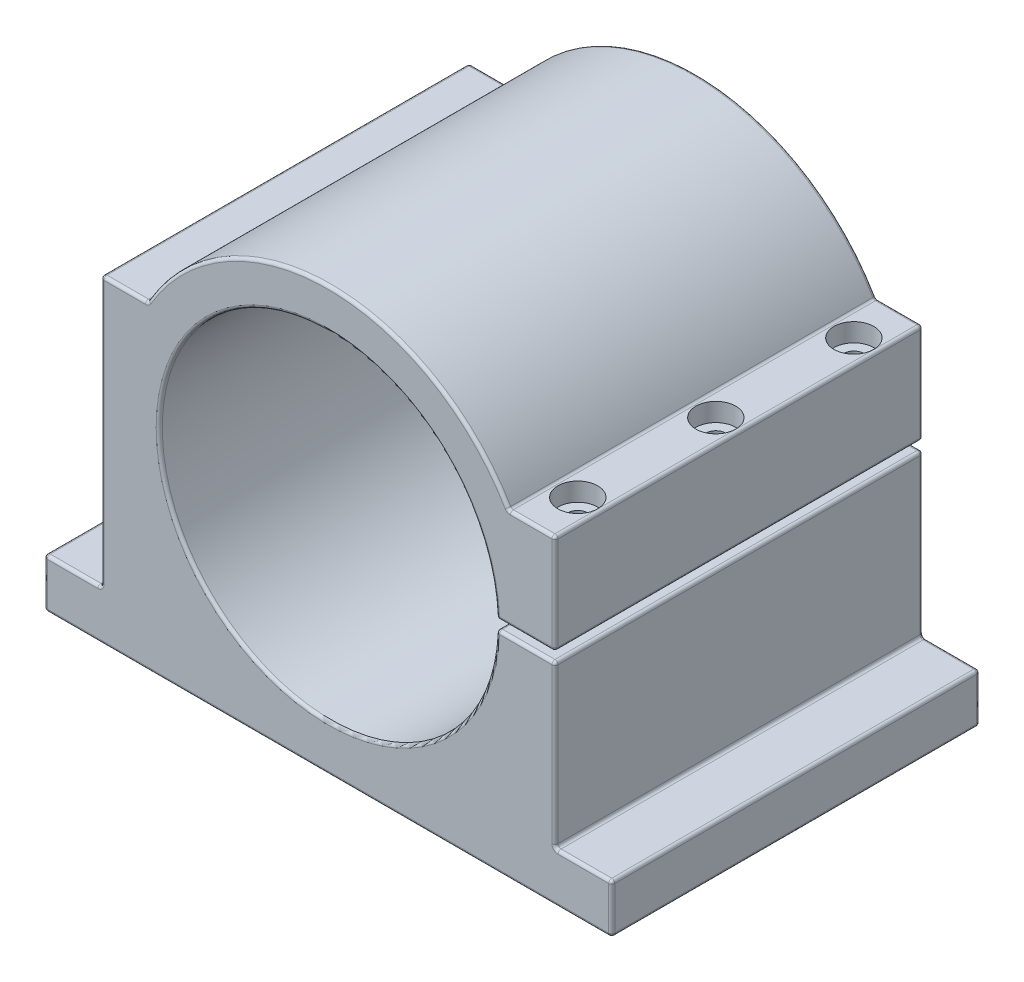
SolidWorks part; units mm, degrees
ref_plane "Спереди" through (0, 0, 0) normal (0, 0, 1) x (1, 0, 0)
ref_plane "Сверху" through (0, 0, 0) normal (0, 1, 0) x (1, 0, 0)
ref_plane "Справа" through (0, 0, 0) normal (1, 0, 0) x (0, 0, -1)
sketch "Эскиз1" plane through (0, 0, 0) normal (0, 0, 1) x (1, 0, 0)
  line L0 (0, 0) -> (0, -70) construction
  line L1 (92.5, -70) -> (-92.5, -70)
  line L2 (-92.5, -70) -> (-92.5, -54)
  line L3 (-92.5, -54) -> (-74, -54)
  line L4 (-74, -54) -> (-74, 34)
  line L5 (-74, 34) -> (-43.2319, 34)
  line L6 (74, 34) -> (43.2319, 34)
  line L7 (74, -54) -> (74, 34)
  line L8 (92.5, -54) -> (74, -54)
  line L9 (92.5, -70) -> (92.5, -54)
  line L11 (0, 1.5) -> (95.6878, 1.5)
  line L12 (0, 1.5) -> (0, -1.5)
  line L13 (0, -1.5) -> (95.6878, -1.5)
  line L14 (95.6878, 1.5) -> (95.6878, -1.5)
  circle A0 centre (0, 0) radius 55
  circle A1 centre (0, 0) radius 68
  point P3 (0, -55)
  point P22 (58.616, 34)
  dimension "D1" = 110
  dimension "D7" = 13
  dimension "D2" = 185
  dimension "D3" = 15
  dimension "D4" = 16
  dimension "D5" = 88
  dimension "D6" = 148
  dimension "D8" = 3
  dimension "D9" = 15.384
extrude "Бобышка-Вытянуть1" add sketch "Эскиз1" along normal mid plane 120 contours L0 A1 L5 L4 L3 L2 L1 | L0 A0 L5 A1 | L6 A1 L5 A0 | L11 A1 L6 A0 | A1 L11 L7 L6 | A1 L0 L1 L9 L8 L7 L13 | A0 L0 A1 L13
sketch "Эскиз2" plane through (0, 34, 0) normal (0, 1, 0) x (1, 0, 0)
  line L0 (66.4449, 60) -> (66.4449, -60) construction
  line L1 (74, 60) -> (58.8897, 60) construction
  line L2 (74, -60) -> (58.8897, -60) construction
  circle A0 centre (66.4449, 45) radius 6.5
  circle A1 centre (66.4449, 0) radius 6.5
  circle A2 centre (66.4449, -45) radius 6.5
  dimension "D3" = 13
  dimension "D1" = 45
  dimension "D2" = 45
extrude "Вырез-Вытянуть1" cut sketch "Эскиз2" against normal blind 6
sketch "Эскиз3" plane through (0, 34, 0) normal (0, 1, 0) x (1, 0, 0)
  circle A0 centre (66.4449, 45) radius 3.25
  circle A1 centre (66.4449, 0) radius 3.25
  circle A2 centre (66.4449, -45) radius 3.25
  dimension "D1" = 6.5
extrude "Вырез-Вытянуть2" cut sketch "Эскиз3" against normal up to surface (35.5 mm away) up to face at (64.4898, -1.5, 0)
sketch "Эскиз4" plane through (0, -1.5, 0) normal (0, 1, 0) x (1, 0, 0)
  circle A0 centre (66.4449, 45) radius 2.35
  circle A1 centre (66.4449, 0) radius 2.35
  circle A2 centre (66.4449, -45) radius 2.35
  dimension "D1" = 4.7
extrude "Вырез-Вытянуть3" cut sketch "Эскиз4" against normal blind 30
fillet "Скругление1" radius 1 42 edges at (-92.5, -54, 0) (-92.5, -70, 0) (-74, -54, 0) (-74, 34, 0) (58.8897, 34, 0) (-58.8897, 34, 0) (74, 1.5, 0) (74, 34, 0) (74, -1.5, 0) (92.5, -70, 0) (92.5, -54, 0) (74, -54, 0) (54.9795, -1.5, 0) (54.9795, 1.5, 0) (-55, 0, -60) (64.4898, 1.5, -60) (74, 17.75, -60) (66.4449, 34, -60) (0, 68, -60) (-66.4449, 34, -60) (-74, -10, -60) (-83.25, -54, -60) (-92.5, -62, -60) (0, -70, -60) (92.5, -62, -60) (83.25, -54, -60) (74, -27.75, -60) (64.4898, -1.5, -60) (74, -27.75, 60) (83.25, -54, 60) (92.5, -62, 60) (0, -70, 60) (-92.5, -62, 60) (-83.25, -54, 60) (-74, -10, 60) (-66.4449, 34, 60) (0, 68, 60) (66.4449, 34, 60) (74, 17.75, 60) (64.4898, 1.5, 60) (-55, 0, 60) (64.4898, -1.5, 60)
